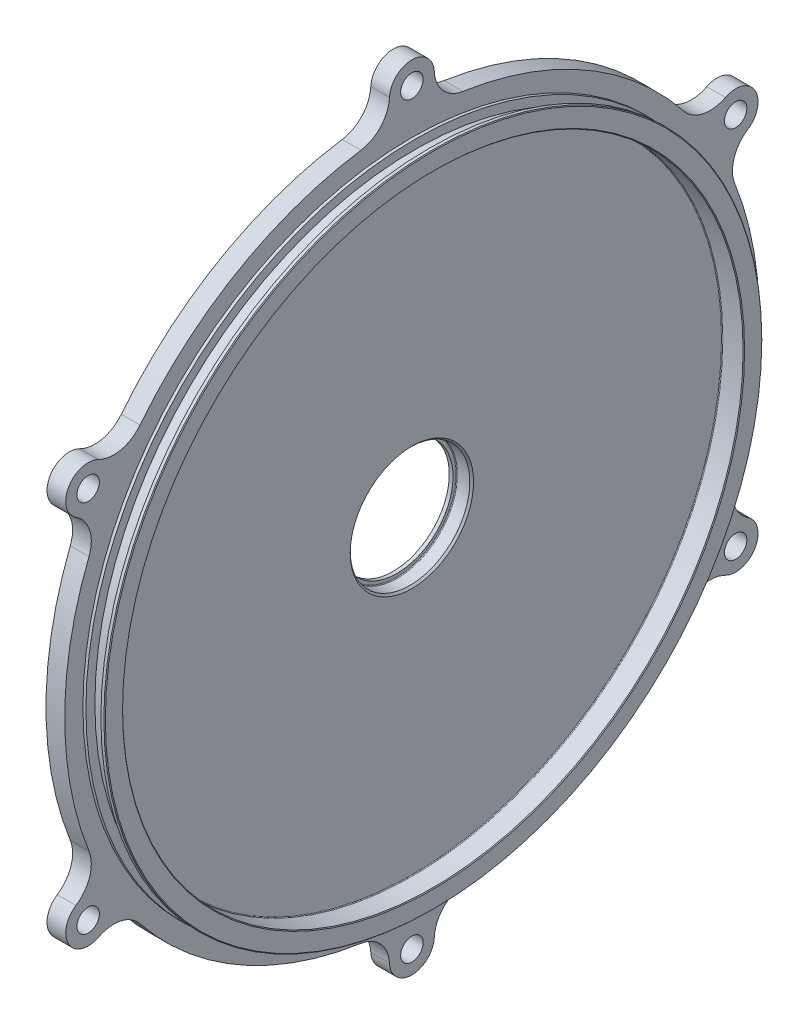
SolidWorks part; units mm, degrees
material "1.7225 (42CrMo4)"
ref_plane "前基準面" through (0, 0, 0) normal (0, 0, 1) x (1, 0, 0)
ref_plane "上基準面" through (0, 0, 0) normal (0, 1, 0) x (1, 0, 0)
ref_plane "右基準面" through (0, 0, 0) normal (1, 0, 0) x (0, 0, -1)
ref_plane "refPlane" through (-7, 0, 0) normal (-1, 0, 0) x (0, 0, 1)
sketch "refSketch" plane through (-7, 0, 0) normal (-1, 0, 0) x (0, 0, 1)
  circle A4 centre (0, 0) radius 92.875
  circle A5 centre (0, 0) radius 86.875
  dimension "D1" = 185.75
  dimension "D2" = 173.75
sketch "Sketch2" plane through (-7, 0, 0) normal (-1, 0, 0) x (0, 0, 1)
  circle A1 centre (0, 0) radius 92.875
  circle A2 centre (0, 0) radius 16
  circle A3 centre (0, 0) radius 92.875 construction
  dimension "D1" = 32
extrude "Boss-Extrude1" add sketch "Sketch2" along normal blind 5
sketch "Sketch3" plane through (-7, 0, 0) normal (-1, 0, 0) x (0, 0, 1)
  line L0 (0, 100) -> (0, 0) construction
  circle A1 centre (0, 0) radius 92.875
  circle A3 centre (0, 100) radius 3
  circle A5 centre (0, 100) radius 6
  circle A8 centre (0, 0) radius 100 construction
  circle A9 centre (0, 0) radius 92.875 construction
  arc A12 (-5.9921, 100.307) -> (-13.6569, 91.8654) centre (-14.9803, 100.7676) cw
  arc A14 (5.9921, 100.307) -> (13.6569, 91.8654) centre (14.9803, 100.7676) ccw
  dimension "D1" = 200
  dimension "D2" = 6
  dimension "D3" = 12
  dimension "D4" = 9
extrude "Boss-Extrude2" add sketch "Sketch3" along normal up to surface (5 mm away) contours A5 A3 | A14 A5 A12 A1
pattern_circular "CirPattern1" count 6 over 360 about axis through (0, 0, 0) along (1, 0, 0) of "Boss-Extrude2"
sketch "Sketch4" plane through (0, 0, 0) normal (1, 0, 0) x (0, 0, -1)
  circle A0 centre (0, 0) radius 15
  circle A1 centre (0, 0) radius 16 construction
  circle A2 centre (0, 0) radius 16
  dimension "D1" = 30
extrude "Boss-Extrude3" add sketch "Sketch4" along normal blind 1 from surface at -12 starting at face at (-12, 0, 0)
fillet "Fillet1" radius 0.2 1 edges at (-11, 0, 16)
chamfer "Chamfer1" distance 0.5 angle 45 1 edges at (-7, 0, 16)
sketch "Sketch5" plane through (-7, 0, 0) normal (-1, 0, 0) x (0, 0, 1)
  circle A1 centre (0, 0) radius 88
  circle A2 centre (0, 0) radius 83
  dimension "D2" = 176
  dimension "D1" = 166
extrude "Boss-Extrude4" add sketch "Sketch5" against normal blind 5.8
chamfer "Chamfer2" distance 0.2 angle 45 2 edges at (-1.2, 0, 88) (-1.2, 0, 83)
fillet "Fillet2" radius 0.2 1 edges at (-7, 0, 83)
sketch "Sketch6" plane through (-7, 0, 0) normal (-1, 0, 0) x (0, 0, 1)
  circle A0 centre (0, 0) radius 85.6
  circle A1 centre (0, 0) radius 88 construction
  circle A2 centre (0, 0) radius 88
  dimension "D1" = 2.4
extrude "Cut-Extrude1" cut sketch "Sketch6" against normal blind 4 from offset 0.8
